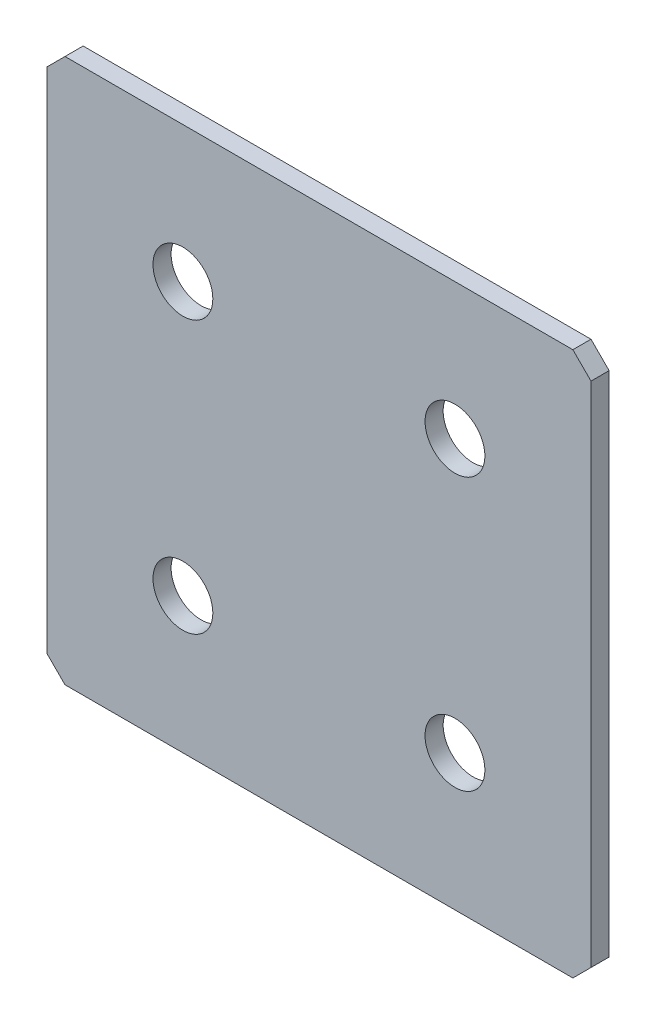
SolidWorks part; units mm, degrees
material "Простая углеродистая сталь"
ref_plane "Спереди(Плоскость XY)" through (0, 0, 0) normal (0, 0, 1) x (1, 0, 0)
ref_plane "Сверху(Плоскость XZ)" through (0, 0, 0) normal (0, 1, 0) x (1, 0, 0)
ref_plane "Справа(Плоскость ZY)" through (0, 0, 0) normal (1, 0, 0) x (0, 0, -1)
sketch "Эскиз1" plane through (0, 0, 0) normal (0, 0, 1) x (1, 0, 0)
  line L1 (-30, -30) -> (30, -30)
  line L2 (-30, -30) -> (-30, 30)
  line L3 (-30, 30) -> (30, 30)
  line L4 (30, -30) -> (30, 30)
  line L5 (-30, -30) -> (30, 30) construction
  line L6 (-30, 30) -> (30, -30) construction
  point P0 (0, 0)
  dimension "D1" = 60
  dimension "D2" = 60
extrude "Бобышка-Вытянуть1" add sketch "Эскиз1" along normal blind 2
chamfer "Фаска1" distance 2 angle 45 4 edges at (-30, -30, 1) (30, -30, 1) (-30, 30, 1) (30, 30, 1)
hole_wizard "Отверстие с зазором M61" positions "Эскиз2" profile "Эскиз3" hole size "M6" standard "DIN" end condition through all
sketch "Эскиз2" plane through (0, 0, 2) normal (0, 0, 1) x (1, 0, 0)
  line L2 (-15, 15) -> (15, 15) construction
  line L3 (-15, 15) -> (-15, 45) construction
  line L4 (-15, 45) -> (15, 45) construction
  line L5 (15, 15) -> (15, 45) construction
  line L7 (-15, -15) -> (15, -15) construction
  line L8 (-15, -15) -> (-15, -45) construction
  line L9 (-15, -45) -> (15, -45) construction
  line L10 (15, -15) -> (15, -45) construction
  line L11 (0, 15) -> (0, -15) construction
  point P0 (-15, 15)
  point P2 (15, 15)
  point P8 (-15, -15)
  point P10 (15, -15)
  point P22 (-15, 45)
  point P24 (15, 45)
  point P93 (15, -45)
  point P170 (-15, -45)
  dimension "D1" = 30
  dimension "D2" = 30
  dimension "D3" = 30
sketch "Эскиз3" plane through (-15, 15, 2) normal (1, 0, 0) x (0, -1, 0)
  line L0 (0, 0) -> (0, 2)
  line L1 (0, 2) -> (3.3, 2)
  line L2 (3.3, 2) -> (3.3, 0)
  line L5 (3.3, 0) -> (0, 0)
  line L11 (0, -6.35) -> (0, 107.95) construction
  dimension "Диаметр сквозного отверстия" = 6.6
  dimension "Глубина сквозного отверстия" = 2
